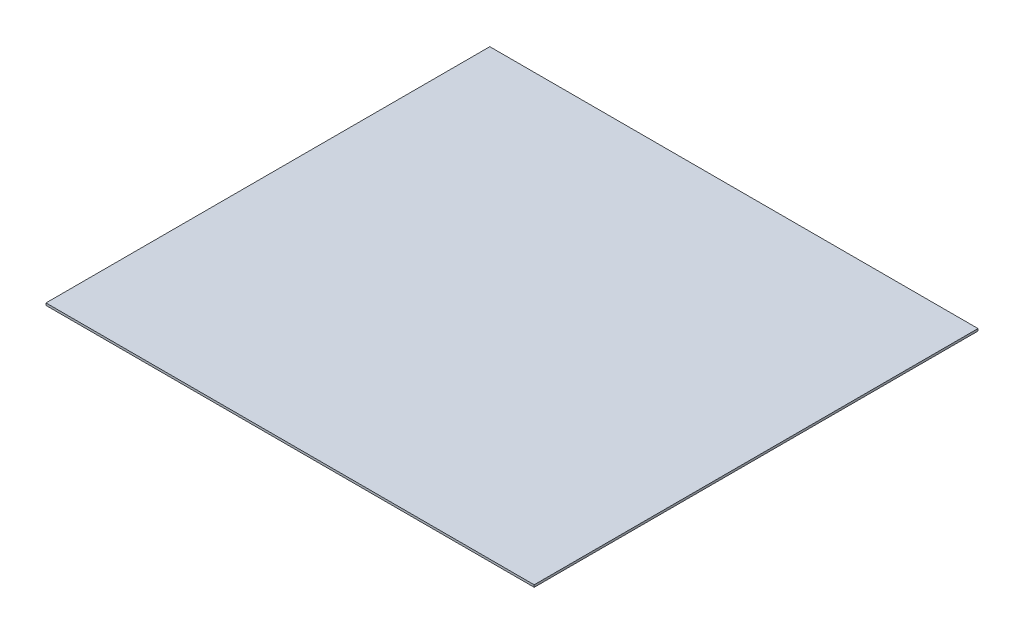
SolidWorks part; units mm, degrees
ref_plane "Plan de face" through (0, 0, 0) normal (0, 0, 1) x (1, 0, 0)
ref_plane "Plan de dessus" through (0, 0, 0) normal (0, 1, 0) x (1, 0, 0)
ref_plane "Plan de droite" through (0, 0, 0) normal (1, 0, 0) x (0, 0, -1)
sketch "Esquisse1" plane through (0, 0, 0) normal (0, 1, 0) x (1, 0, 0)
  line L1 (0, 0) -> (2200, 0)
  line L2 (0, 0) -> (0, 2000)
  line L3 (0, 2000) -> (2200, 2000)
  line L4 (2200, 0) -> (2200, 2000)
  dimension "D1" = 2000
  dimension "D2" = 2200
extrude "Extrusion1" add sketch "Esquisse1" along normal blind 10
